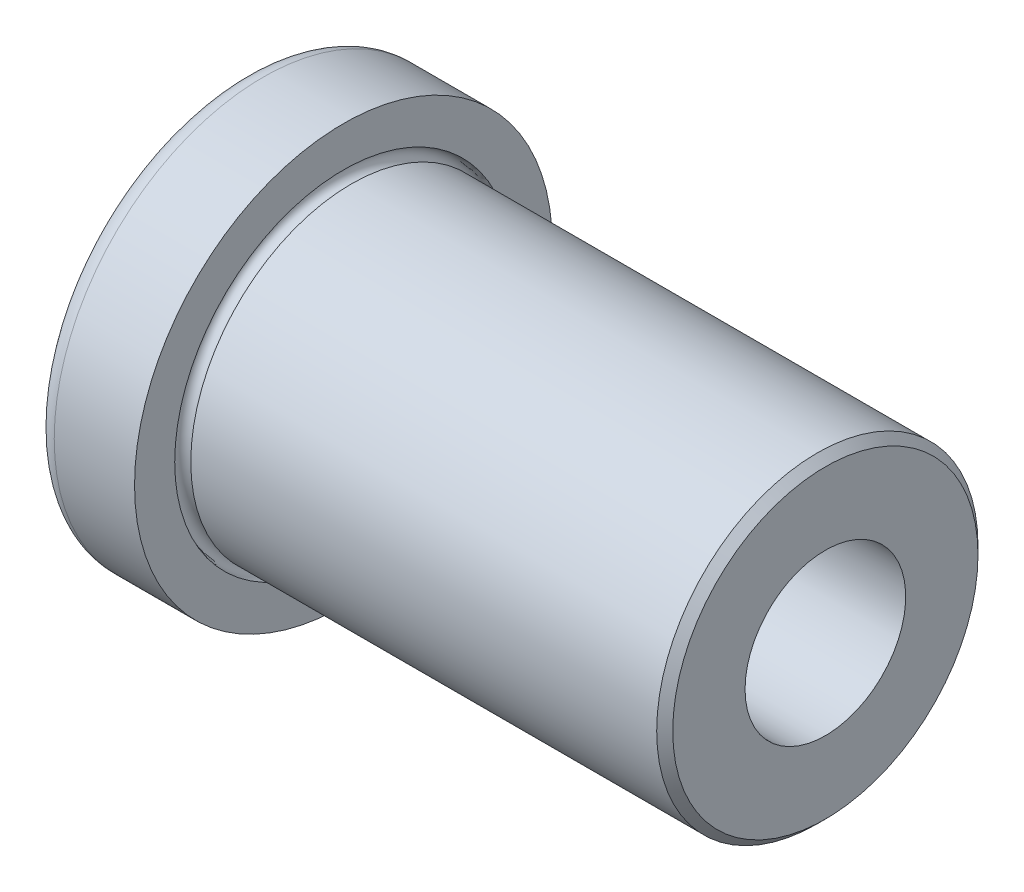
SolidWorks part; units mm, degrees
material "Alloy Steel"
ref_plane "Plane1" through (0, 0, 0) normal (0, 0, 1) x (1, 0, 0)
ref_plane "Plane2" through (0, 0, 0) normal (0, 1, 0) x (1, 0, 0)
ref_plane "Plane3" through (0, 0, 0) normal (1, 0, 0) x (0, 0, -1)
sketch "Sketch1" plane through (0, 0, 0) normal (0, 0, 1) x (1, 0, 0)
  line L0 (0, 0) -> (76.2, 0) construction
  line L1 (0, 3.9624) -> (0, 7.4676)
  line L2 (0.7874, 8.255) -> (3.9624, 8.255)
  line L3 (3.9624, 8.255) -> (3.9624, 6.6675)
  line L4 (4.2799, 6.35) -> (22.6949, 6.35)
  line L5 (22.6949, 6.35) -> (23.0124, 6.0325)
  line L6 (23.0124, 6.0325) -> (23.0124, 3.175)
  line L7 (23.0124, 3.175) -> (0.7874, 3.175)
  line L8 (22.6949, -6.35) -> (23.0124, -6.0325) construction
  line L9 (23.0124, -3.175) -> (0, -3.175) construction
  line L10 (4.2799, -6.35) -> (22.6949, -6.35) construction
  line L11 (0, -8.255) -> (3.9624, -8.255) construction
  arc A0 (3.9624, 6.6675) -> (4.2799, 6.35) centre (3.9624, 6.35) ccw
  arc A1 (0, 3.9624) -> (0.7874, 3.175) centre (0.7874, 3.9624) ccw
  arc A2 (0.7874, 8.255) -> (0, 7.4676) centre (0.7874, 7.4676) ccw
  point P20 (0, 3.175)
  point P23 (0, 8.255)
  dimension "Head_radii" = 0.7874
  dimension "D1" = 0.3175
  dimension "Hole_dia" = 6.35
  dimension "Body_dia" = 12.7
  dimension "Body_len" = 19.05
  dimension "Head_dia" = 16.51
  dimension "Head_ht" = 3.9624
  dimension "D2" = 12.065
  dimension "D3" = 45
revolve "BaseBody" add sketch "Sketch1" angle 360 about L0
equation "\"D1@Sketch1\" =  ( \"Body_dia@Sketch1\" -  ( \"Body_dia@Sketch1\" * .9 )  )  / 4"
equation "\"D2@Sketch1\" = \"Body_dia@Sketch1\" -  ( \"D1@Sketch1\" * 2 ) "
